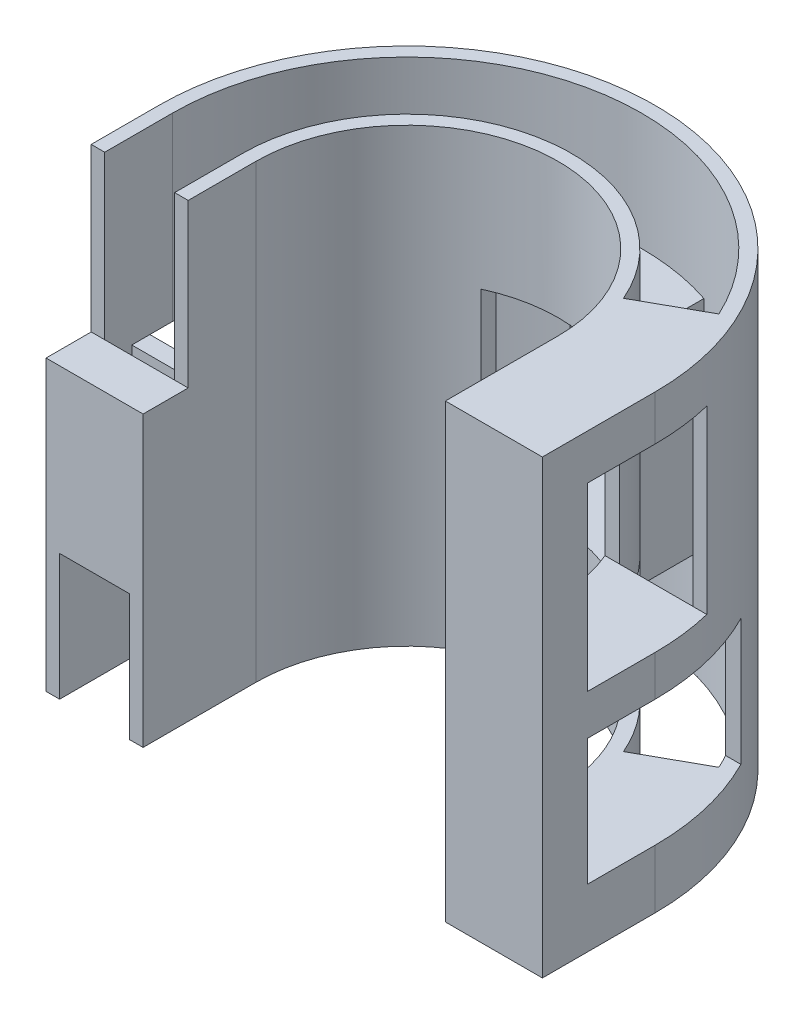
SolidWorks part; units mm, degrees
ref_plane "Front Plane" through (0, 0, 0) normal (0, 0, 1) x (1, 0, 0)
ref_plane "Top Plane" through (0, 0, 0) normal (0, 1, 0) x (1, 0, 0)
ref_plane "Right Plane" through (0, 0, 0) normal (1, 0, 0) x (0, 0, -1)
sketch "Sketch2" plane through (0, 0, 0) normal (0, 1, 0) x (1, 0, 0)
  circle A0 centre (0, 0) radius 27.5
  dimension "D1" = 55
extrude "Boss-Extrude1" add sketch "Sketch2" along normal blind 50 contours A0
sketch "Sketch3" plane through (0, 50, 0) normal (0, 1, 0) x (1, 0, 0)
  circle A0 centre (0, 0) radius 26
  dimension "D1" = 52
extrude "Cut-Extrude1" cut sketch "Sketch3" against normal through all
sketch "Sketch7" plane through (0, 50, 0) normal (0, 1, 0) x (1, 0, 0)
  circle A0 centre (0, 0) radius 18.25
  dimension "D1" = 36.5
extrude "Boss-Extrude3" add sketch "Sketch7" against normal blind 50 separate body
sketch "Sketch8" plane through (0, 50, 0) normal (0, 1, 0) x (1, 0, 0)
  circle A0 centre (0, 0) radius 16.75
  dimension "D1" = 33.5
extrude "Cut-Extrude3" cut sketch "Sketch8" against normal through all
sketch "Sketch9" plane through (0, 50, 0) normal (0, 1, 0) x (1, 0, 0)
  line L1 (-30.4577, 0) -> (29.5035, 0)
  line L2 (-30.4577, 0) -> (-30.4577, -28.5161)
  line L3 (-30.4577, -28.5161) -> (29.5035, -28.5161)
  line L4 (29.5035, 0) -> (29.5035, -28.5161)
extrude "Cut-Extrude4" cut sketch "Sketch9" against normal through all
sketch "Sketch10" plane through (0, 50, 0) normal (0, 1, 0) x (1, 0, 0)
  line L0 (-27.5, 0) -> (-27.5, -12.5)
  line L1 (-26, 0) -> (-27.5, 0) construction
  line L2 (-26, 0) -> (-26, -12.5)
  line L3 (-26, -12.5) -> (-27.5, -12.5)
  line L4 (-27.5, 0) -> (-26, 0)
  line L10 (-18.25, 0) -> (-16.75, 0)
  line L11 (-16.75, 0) -> (-18.25, 0) construction
  line L12 (-16.75, 0) -> (-16.75, -12.5)
  line L13 (-16.75, -12.5) -> (-18.25, -12.5)
  line L14 (-18.25, -12.5) -> (-18.25, 0)
  line L15 (16.75, 0) -> (18.25, 0)
  line L16 (18.25, 0) -> (18.25, -12.5)
  line L17 (18.25, -12.5) -> (16.75, -12.5)
  line L18 (16.75, -12.5) -> (16.75, 0)
  line L19 (27.5, 0) -> (26, 0)
  line L20 (26, 0) -> (26, -12.5)
  line L21 (26, -12.5) -> (27.5, -12.5)
  line L22 (27.5, -12.5) -> (27.5, 0)
  arc A0 (27.5, 0) -> (-27.5, 0) centre (0, 0) ccw construction
  arc A2 (16.75, 0) -> (-16.75, 0) centre (0, 0) ccw construction
  arc A3 (18.25, 0) -> (-18.25, 0) centre (0, 0) ccw construction
  dimension "D1" = 12.5
  dimension "D2" = 12.5
  dimension "D3" = 12.5
  dimension "D4" = 12.5
extrude "Boss-Extrude4" add sketch "Sketch10" against normal blind 50
sketch "Sketch11" plane through (0, 50, 0) normal (0, 1, 0) x (1, 0, 0)
  line L16 (18.25, -12.5) -> (18.25, 0) construction
  line L17 (16.7607, 7.2208) -> (23.5569, 11.0033)
  line L18 (18.25, 0) -> (18.25, -12.5)
  line L19 (18.25, -12.5) -> (26, -12.5)
  line L20 (26, -12.5) -> (26, 0)
  arc A4 (18.25, 0) -> (16.7607, 7.2208) centre (0, 0) ccw
  arc A5 (18.25, 0) -> (-18.25, 0) centre (0, 0) ccw construction
  arc A6 (26, 0) -> (23.5569, 11.0033) centre (0, 0) ccw
extrude "Boss-Extrude5" add sketch "Sketch11" against normal blind 5
sketch "Sketch12" plane through (27.5, 0, 0) normal (1, 0, 0) x (0, 0, -1)
  line L0 (-7.5, 45) -> (-7.5, 25)
  line L1 (-7.5, 25) -> (6.5, 25)
  line L2 (6.5, 25) -> (6.5, 45)
  line L3 (6.5, 45) -> (-7.5, 45)
  line L4 (-12.5, 0) -> (-12.5, 50) construction
  line L5 (27.5, 50) -> (0, 50) construction
  line L6 (-7.5, 20.5) -> (-7.5, 6.5)
  line L7 (-7.5, 6.5) -> (12.5, 6.5)
  line L8 (12.5, 6.5) -> (12.5, 20.5)
  line L9 (12.5, 20.5) -> (-7.5, 20.5)
  line L10 (-12.5, 0) -> (0, 0) construction
  dimension "D1" = 20
  dimension "D2" = 14
  dimension "D3" = 5
  dimension "D4" = 5
  dimension "D5" = 14
  dimension "D6" = 20
  dimension "D7" = 6.5
sketch "Sketch13" plane through (0, 0, 0) normal (0, -1, 0) x (1, 0, 0)
  line L0 (23.5569, -11.0033) -> (16.7607, -7.2208) construction
  line L1 (18.25, 0) -> (18.25, 12.5)
  line L2 (18.25, 12.5) -> (26, 12.5)
  line L3 (26, 12.5) -> (26, 0)
  line L4 (16.7607, -7.2208) -> (23.5569, -11.0033)
  arc A0 (18.25, 0) -> (16.7607, -7.2208) centre (0, 0) cw
  arc A3 (23.5569, -11.0033) -> (26, 0) centre (0, 0) ccw
  arc A4 (-26, 0) -> (26, 0) centre (0, 0) ccw construction
extrude "Boss-Extrude6" add sketch "Sketch13" against normal blind 6.5
extrude "Cut-Extrude6" cut sketch "Sketch12" against normal blind 15
sketch "Sketch14" plane through (0, 0, 12.5) normal (0, 0, 1) x (1, 0, 0)
  line L0 (7, 35) -> (7, 15)
  line L1 (7, 15) -> (-7, 15)
  line L2 (-7, 15) -> (-7, 35)
  line L3 (-7, 35) -> (7, 35)
  line L4 (16.75, 50) -> (-16.75, 50) construction
  dimension "D1" = 7
  dimension "D2" = 14
  dimension "D3" = 20
  dimension "D4" = 15
extrude "Cut-Extrude7" cut sketch "Sketch14" against normal blind 45
sketch "Sketch15" plane through (-27.5, 0, 0) normal (-1, 0, 0) x (0, 0, 1)
  line L0 (0, 0) -> (12.5, 0) construction
  line L1 (7.5, 54.2356) -> (24.1059, 54.2356)
  line L2 (7.5, 54.2356) -> (7.5, 32)
  line L3 (7.5, 32) -> (24.1059, 32)
  line L4 (24.1059, 54.2356) -> (24.1059, 32)
  line L5 (12.5, 0) -> (12.5, 50) construction
  dimension "D1" = 32
  dimension "D2" = 5
extrude "Cut-Extrude8" cut sketch "Sketch15" against normal blind 15
sketch "Sketch17" plane through (0, 25, 0) normal (0, 1, 0) x (1, 0, 0)
  line L0 (15.4374, 6.5) -> (17.0532, 6.5) construction
  line L1 (25.1744, 6.5) -> (26.7208, 6.5) construction
  line L2 (26.7208, 6.5) -> (17.0532, 6.5)
  line L3 (27.5, 0) -> (27.5, -7.5)
  line L4 (27.5, -7.5) -> (18.25, -7.5)
  line L5 (18.25, -7.5) -> (18.25, 0)
  arc A0 (18.25, 0) -> (17.0532, 6.5) centre (0, 0) ccw
  arc A1 (27.5, 0) -> (26.7208, 6.5) centre (0, 0) ccw
extrude "Boss-Extrude8" add sketch "Sketch17" against normal blind 4.5
sketch "Sketch18" plane through (0, 35, 0) normal (0, -1, 0) x (1, 0, 0)
  line L0 (7, -26.5942) -> (7, -25.04) construction
  line L1 (-7, -16.8542) -> (-7, -25.04)
  line L2 (7, -16.8542) -> (7, -25.04)
  arc A0 (-7, -16.8542) -> (7, -16.8542) centre (0, 0) ccw
  arc A1 (-7, -16.8542) -> (7, -16.8542) centre (0, 0) ccw construction
  arc A2 (-7, -25.04) -> (7, -25.04) centre (0, 0) ccw
extrude "Boss-Extrude9" add sketch "Sketch18" against normal blind 2
sketch "Sketch19" plane through (0, 15, 0) normal (0, 1, 0) x (1, 0, 0)
  line L0 (7, 16.8542) -> (7, 15.2172) construction
  line L1 (7, 25.04) -> (7, 16.8542)
  line L2 (-7, 25.04) -> (-7, 16.8542)
  arc A0 (-7, 16.8542) -> (7, 16.8542) centre (0, 0) cw
  arc A1 (-7, 25.04) -> (7, 25.04) centre (0, 0) cw
  arc A2 (7, 25.04) -> (-7, 25.04) centre (0, 0) ccw construction
extrude "Boss-Extrude10" add sketch "Sketch19" against normal blind 2
sketch "Sketch24" plane through (0, 37, 0) normal (0, 1, 0) x (1, 0, 0)
  line L0 (8.2373, 24.6606) -> (8.2373, 16.2852)
  line L1 (7, 25.04) -> (7, 16.8542)
  arc A1 (7, 25.04) -> (8.2373, 24.6606) centre (0, 0) cw
  arc A3 (7, 16.8542) -> (8.2373, 16.2852) centre (0, 0) cw
extrude "Boss-Extrude15" add sketch "Sketch24" against normal blind 24
sketch "Sketch25" plane through (27.5, 0, 0) normal (1, 0, 0) x (0, 0, -1)
  line L1 (-12.5, 0) -> (-12.5, 50) construction
  line L2 (-7.5, 45) -> (-12.5, 45)
  line L3 (-7.5, 25) -> (-7.5, 45)
  line L4 (-12.5, 45) -> (-12.5, 25)
  line L5 (-7.5, 25) -> (-7.5, 20.5)
  line L6 (-7.5, 20.5) -> (-12.5, 20.5)
  line L7 (-12.5, 20.5) -> (-12.5, 25)
extrude "Boss-Extrude17" add sketch "Sketch25" against normal blind 10
sketch "Sketch26" plane through (-27.5, 0, 0) normal (-1, 0, 0) x (0, 0, 1)
  line L0 (12.5, 32) -> (7.5, 32)
  line L1 (7.5, 32) -> (7.5, 14)
  line L2 (7.5, 14) -> (12.5, 14)
  line L3 (12.5, 0) -> (12.5, 32) construction
  line L4 (12.5, 14) -> (12.5, 32)
  dimension "D1" = 18
extrude "Boss-Extrude18" add sketch "Sketch26" against normal blind 10
sketch "Sketch27" plane through (0, 0, 12.5) normal (0, 0, 1) x (1, 0, 0)
  line L1 (18.25, 20.5) -> (26, 20.5)
  line L2 (18.25, 20.5) -> (18.25, 6.5)
  line L3 (18.25, 6.5) -> (26, 6.5)
  line L4 (26, 20.5) -> (26, 6.5)
extrude "Boss-Extrude19" add sketch "Sketch27" against normal blind 5
sketch "Sketch29" plane through (-27.5, 0, 0) normal (-1, 0, 0) x (0, 0, 1)
  line L0 (0, 0) -> (12.5, 0) construction
  line L1 (2.5, 10) -> (-11.5, 10)
  line L2 (2.5, 10) -> (2.5, 30)
  line L3 (2.5, 30) -> (-11.5, 30)
  line L4 (-11.5, 10) -> (-11.5, 30)
  line L5 (12.5, 0) -> (12.5, 32) construction
  dimension "D1" = 14
  dimension "D2" = 20
  dimension "D3" = 10
  dimension "D4" = 10
extrude "Cut-Extrude9" cut sketch "Sketch29" against normal blind 8
sketch "Sketch30" plane through (-27.5, 0, 0) normal (-1, 0, 0) x (0, 0, 1)
  line L0 (2.5, 10) -> (4.5, 10)
  line L1 (2.5, 30) -> (4.5, 30)
  line L2 (4.5, 30) -> (4.5, 10)
  line L3 (2.5, 10) -> (2.5, 30)
  dimension "D1" = 2
extrude "Boss-Extrude20" add sketch "Sketch30" against normal blind 10
